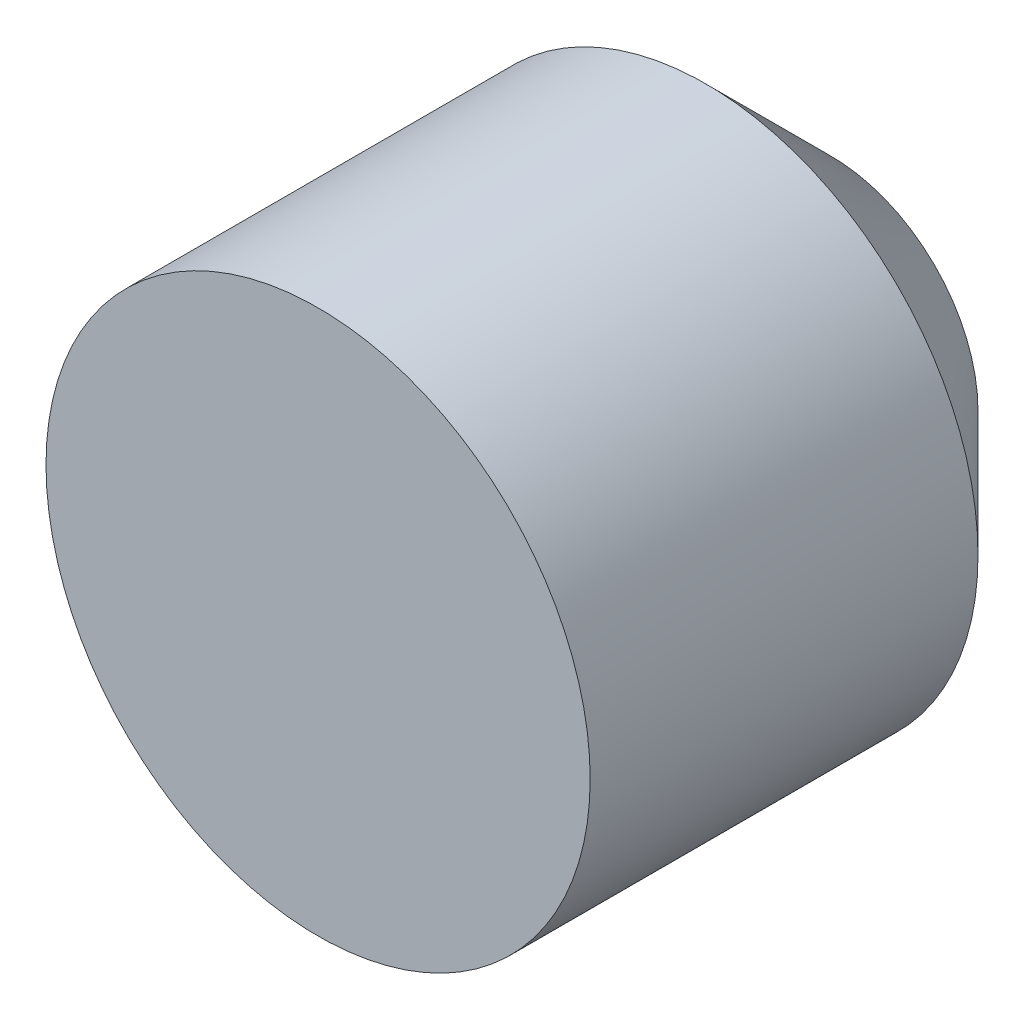
SolidWorks part; units mm, degrees
material "6061-T6 (SS)"
ref_plane "Front Plane" through (0, 0, 0) normal (0, 0, 1) x (1, 0, 0)
ref_plane "Top Plane" through (0, 0, 0) normal (0, 1, 0) x (1, 0, 0)
ref_plane "Right Plane" through (0, 0, 0) normal (1, 0, 0) x (0, 0, -1)
sketch "Sketch1" plane through (0, 0, 0) normal (0, 0, 1) x (1, 0, 0)
  circle A0 centre (0, 0) radius 21.75
  dimension "D1" = 43.5
extrude "Boss-Extrude1" add sketch "Sketch1" along normal blind 41
chamfer "Chamfer1" distance 10 angle 45 1 edges at (21.75, 0, 0)
